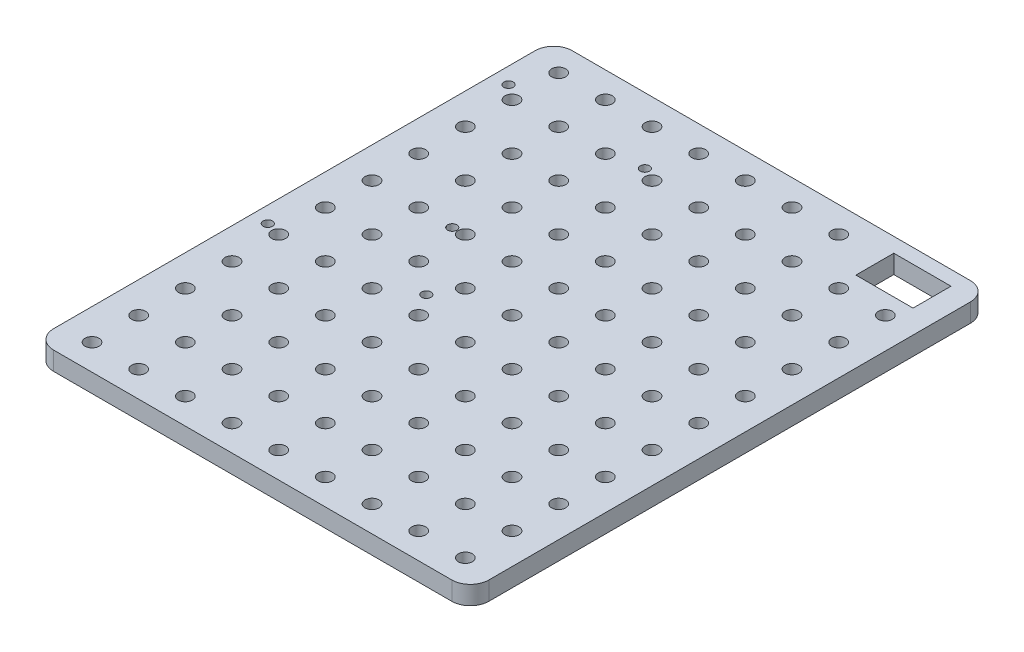
SolidWorks part; units mm, degrees
ref_plane "Front Plane" through (0, 0, 0) normal (0, 0, 1) x (1, 0, 0)
ref_plane "Top Plane" through (0, 0, 0) normal (0, 1, 0) x (1, 0, 0)
ref_plane "Right Plane" through (0, 0, 0) normal (1, 0, 0) x (0, 0, -1)
sketch "Sketch2" plane through (0, 0, 0) normal (0, 1, 0) x (1, 0, 0)
  line L1 (-74.6125, -88.9) -> (74.6125, -88.9)
  line L3 (-74.6125, 88.9) -> (74.6125, 88.9)
  line L5 (-74.6125, -88.9) -> (74.6125, 88.9) construction
  line L6 (-74.6125, 88.9) -> (74.6125, -88.9) construction
  line L9 (-74.6125, -88.9) -> (-74.6125, 88.9)
  line L10 (0, -88.9) -> (0, 88.9) construction
  line L14 (74.6125, -88.9) -> (74.6125, 88.9)
  point P0 (0, 0)
  dimension "D1" = 149.225
  dimension "D2" = 177.8
extrude "Boss-Extrude1" add sketch "Sketch2" along normal blind 6.35
fillet "Fillet1" radius 6.35 4 edges at (74.6125, 3.175, -88.9) (-74.6125, 3.175, -88.9) (74.6125, 3.175, 88.9) (-74.6125, 3.175, 88.9)
sketch "Sketch3" plane through (0, 6.35, 0) normal (0, 1, 0) x (1, 0, 0)
  circle A0 centre (-64, 80) radius 2.4
  dimension "D3" = 4.8
  dimension "D1" = 64
  dimension "D2" = 80
extrude "Cut-Extrude2" cut sketch "Sketch3" against normal through all
pattern_linear "LPattern2" count 9 spacing 16 along (1, 0, 0) count 11 spacing 16 along (0, 0, 1) skipping (7, 0), (8, 0) of "Cut-Extrude2"
sketch "Sketch4" plane through (0, 6.35, 0) normal (0, 1, 0) x (1, 0, 0)
  line L1 (-71.58, -19.7) -> (-18.28, -19.7) construction
  line L2 (-71.58, -19.7) -> (-71.58, 81.9) construction
  line L3 (-71.58, 81.9) -> (-18.28, 81.9) construction
  line L4 (-18.28, -19.7) -> (-18.28, 81.9) construction
  line L6 (68.2625, 88.9) -> (-68.2625, 88.9) construction
  circle A0 centre (-69.08, 67.9) radius 1.6
  circle A1 centre (-20.82, 66.376) radius 1.6
  circle A2 centre (-20.82, -8.554) radius 1.6
  circle A3 centre (-69.08, -14.65) radius 1.6
  circle A4 centre (-64, 15.83) radius 1.6
  circle A5 centre (-36.314, 15.83) radius 1.6
  point P12 (-36.314, 15.83)
  point P13 (-64, 15.83)
  dimension "D12" = 3.2
  dimension "D10" = 82.55
  dimension "D7" = 52.07
  dimension "D3" = 32.766
  dimension "D14" = 7
  dimension "D4" = 5.08
  dimension "D6" = 76.454
  dimension "D11" = 48.26
  dimension "D5" = 2.5
  dimension "D1" = 101.6
  dimension "D2" = 53.3
  dimension "D8" = 14
  dimension "D9" = 1.524
extrude "MOUNTING_HOLES" cut sketch "Sketch4" against normal through all
sketch "Sketch5" plane through (0, 6.35, 0) normal (0, 1, 0) x (1, 0, 0)
  line L0 (68.2625, 88.9) -> (-68.2625, 88.9) construction
  line L1 (47.0125, 83.9) -> (66.6125, 83.9)
  line L2 (47.0125, 83.9) -> (47.0125, 70.9)
  line L3 (47.0125, 70.9) -> (66.6125, 70.9)
  line L4 (66.6125, 83.9) -> (66.6125, 70.9)
  line L5 (74.6125, -82.55) -> (74.6125, 82.55) construction
  dimension "D1" = 13
  dimension "D2" = 19.6
  dimension "D3" = 5
  dimension "D4" = 8
extrude "SWITCH_CUTOUT" cut sketch "Sketch5" against normal through all
equation "\"D1@Sketch3\"=4*16"
equation "\"D2@Sketch3\"=5*16"
